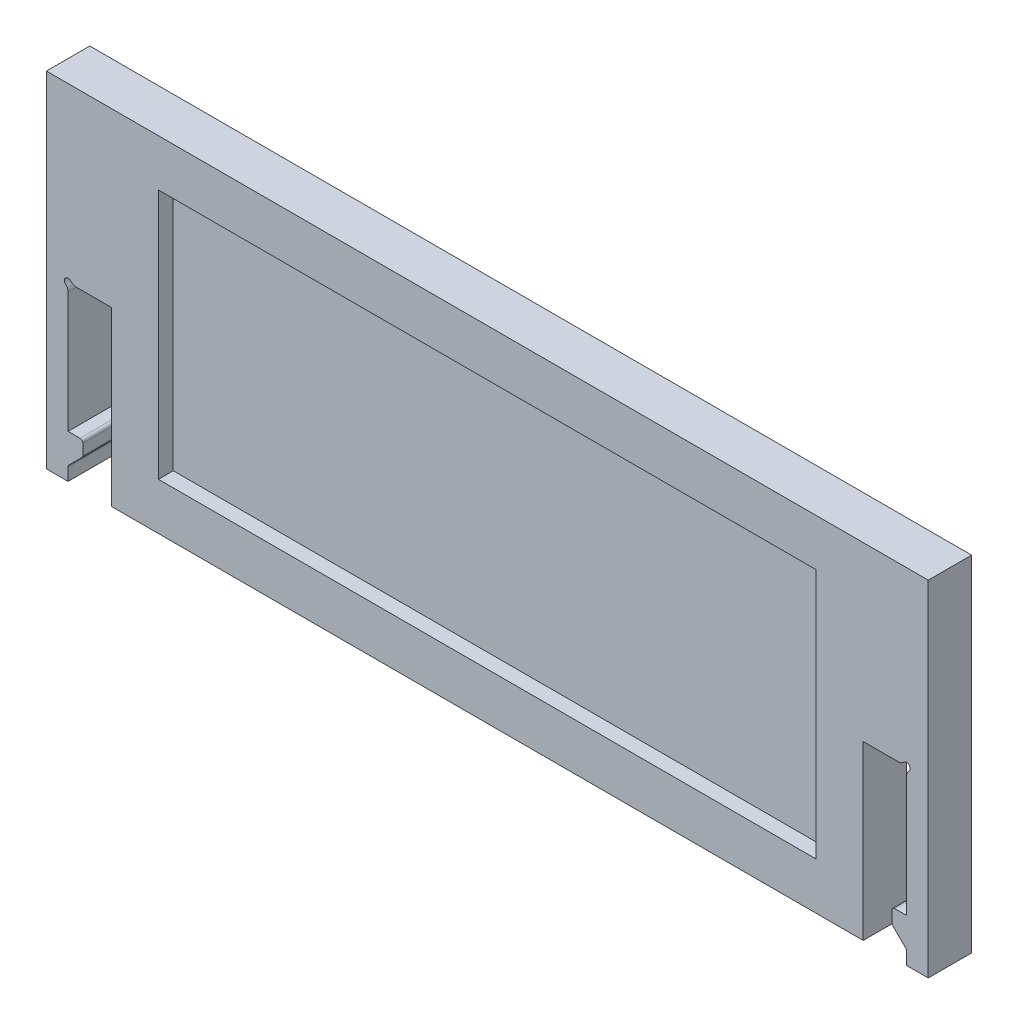
SolidWorks part; units mm, degrees
ref_plane "Front Plane" through (0, 0, 0) normal (0, 0, 1) x (1, 0, 0)
ref_plane "Top Plane" through (0, 0, 0) normal (0, 1, 0) x (1, 0, 0)
ref_plane "Right Plane" through (0, 0, 0) normal (1, 0, 0) x (0, 0, -1)
sketch "Sketch1" plane through (0, 0, 0) normal (0, 0, 1) x (1, 0, 0)
  line L1 (-29.795, 11.6417) -> (29.795, 11.6417)
  line L2 (-29.795, 11.6417) -> (-29.795, -11.6417)
  line L3 (-29.795, -11.6417) -> (29.795, -11.6417)
  line L4 (29.795, 11.6417) -> (29.795, -11.6417)
  line L5 (-29.795, 11.6417) -> (29.795, -11.6417) construction
  line L6 (-29.795, -11.6417) -> (29.795, 11.6417) construction
  point P0 (0, 0)
  dimension "D1" = 23.2833
  dimension "D2" = 59.59
extrude "Boss-Extrude1" add sketch "Sketch1" along normal blind 2.93
sketch "Sketch2" plane through (0, 0, 2.93) normal (0, 0, 1) x (1, 0, 0)
  line L0 (-29.795, -11.6417) -> (29.795, -11.6417) construction
  line L1 (-28.33, -11.6417) -> (-25.4, -11.6417)
  line L2 (-28.33, -11.6417) -> (-28.33, 0)
  line L3 (-28.33, 0) -> (-25.4, 0)
  line L4 (-25.4, -11.6417) -> (-25.4, 0)
  line L5 (-29.795, 11.6417) -> (-29.795, -11.6417) construction
  dimension "D1" = 2.93
  dimension "D2" = 1.465
extrude "Cut-Extrude1" cut sketch "Sketch2" against normal through all
sketch "Sketch4" plane through (0, 0, 2.93) normal (0, 0, 1) x (1, 0, 0)
  line L0 (-28.33, 0) -> (-28.33, -11.6417) construction
  line L1 (-25.4, -11.6417) -> (-28.33, -11.6417) construction
  line L2 (-25.4, -11.6417) -> (-25.4, -8.7117) construction
  line L3 (-25.4, -8.7117) -> (-28.33, -8.7117) construction
  line L4 (-28.33, -11.6417) -> (-28.33, -8.7117) construction
  line L5 (-28.33, -8.7117) -> (-27.33, -8.7117)
  line L6 (-27.33, -8.7117) -> (-27.33, -9.7117)
  line L7 (-27.33, -9.7117) -> (-28.33, -10.7117)
  line L8 (-28.33, -8.7117) -> (-28.33, -10.7117)
  line M8 (-28.33, -11.6417) -> (-28.33, 0)
  dimension "D1" = 1
  dimension "D2" = 1
  dimension "D3" = 135
extrude "Boss-Extrude3" add sketch "Sketch4" against normal up to surface (2.93 mm away) contours L7 L6 L5 M8 up to face at (-13.4325, -2.9104, 0)
fillet "Fillet1" radius 0.2 3 edges at (-27.33, -8.7117, 1.465) (-27.33, -9.7117, 1.465) (-28.33, -10.7117, 1.465)
sketch "Sketch5" plane through (0, 0, 2.93) normal (0, 0, 1) x (1, 0, 0)
  circle A0 centre (-28.33, 0) radius 0.25
  dimension "D1" = 0.5
extrude "Cut-Extrude3" cut sketch "Sketch5" against normal through all
fillet "Fillet2" radius 0.5 2 edges at (-28.08, 0, 1.465) (-28.33, -0.25, 1.465)
mirror "Mirror1" about plane through (0, 0, 0) normal (1, 0, 0) of "Fillet2", "Cut-Extrude3", "Fillet1", "Boss-Extrude3", "Cut-Extrude1"
sketch "Sketch3" plane through (0, 0, 2.93) normal (0, 0, 1) x (1, 0, 0)
  line L1 (-22.225, 8.4667) -> (22.225, 8.4667)
  line L2 (-22.225, 8.4667) -> (-22.225, -8.4667)
  line L3 (-22.225, -8.4667) -> (22.225, -8.4667)
  line L4 (22.225, 8.4667) -> (22.225, -8.4667)
  line L5 (-22.225, 8.4667) -> (22.225, -8.4667) construction
  line L6 (-22.225, -8.4667) -> (22.225, 8.4667) construction
  point P0 (0, 0)
  dimension "D1" = 44.45
  dimension "D2" = 16.9333
extrude "Cut-Extrude2" cut sketch "Sketch3" against normal blind 1
equation "\"thick\"= 2.93mm'Acrylic thickness"
equation "\"slot\"= 10mm'Slot width"
equation "\"D2@Sketch1\"=3 * \"thick\" + 2"
equation "\"D1@Boss-Extrude1\"=\"thick\""
equation "\"D1@Sketch2\"=\"thick\""
equation "\"D2@Sketch2\"=\"thick\" / 2"
equation "\"D1@Sketch1\"=(2/3)+1/4"
